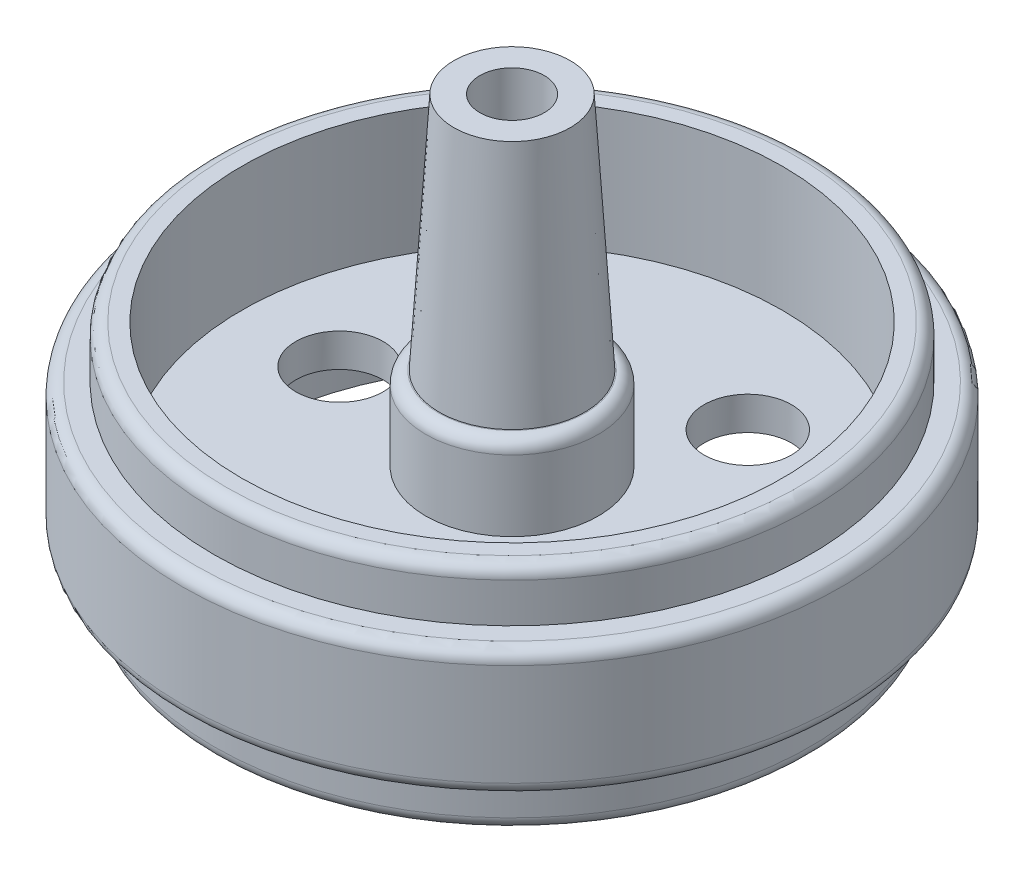
SolidWorks part; units mm, degrees
ref_plane "Front Plane" through (0, 0, 0) normal (0, 0, 1) x (1, 0, 0)
ref_plane "Top Plane" through (0, 0, 0) normal (0, 1, 0) x (1, 0, 0)
ref_plane "Right Plane" through (0, 0, 0) normal (1, 0, 0) x (0, 0, -1)
sketch "Sketch1" plane through (0, 0, 0) normal (0, 1, 0) x (1, 0, 0)
  circle A0 centre (0, 0) radius 14.35
  dimension "D1" = 28.7
extrude "Boss-Extrude1" add sketch "Sketch1" along normal blind 2.5
sketch "Sketch2" plane through (0, 2.5, 0) normal (0, 1, 0) x (1, 0, 0)
  circle A0 centre (0, 0) radius 15.85
  dimension "D1" = 31.7
extrude "Boss-Extrude2" add sketch "Sketch2" along normal blind 6.1
sketch "Sketch4" plane through (0, 8.6, 0) normal (0, 1, 0) x (1, 0, 0)
  circle A0 centre (0, 0) radius 14.35
  dimension "D1" = 28.7
extrude "Boss-Extrude4" add sketch "Sketch4" along normal blind 2.5
sketch "Sketch5" plane through (0, 0, 0) normal (0, -1, 0) x (1, 0, 0)
  circle A0 centre (0, 0) radius 13.05
  circle A1 centre (0, 0) radius 4.3
  dimension "D1" = 26.1
  dimension "D2" = 8.6
sketch "Sketch6" plane through (0, 11.1, 0) normal (0, 1, 0) x (1, 0, 0)
  circle A0 centre (0, 0) radius 13
  dimension "D1" = 26
extrude "Cut-Extrude1" cut sketch "Sketch6" against normal blind 6
extrude "Cut-Extrude2" cut sketch "Sketch5" against normal blind 3.5
sketch "Sketch7" plane through (0, 5.1, 0) normal (0, 1, 0) x (1, 0, 0)
  circle A0 centre (0, 0) radius 4.15
  dimension "D1" = 8.3
extrude "Boss-Extrude5" add sketch "Sketch7" along normal blind 4
sketch "Sketch8" plane through (0, 9.1, 0) normal (0, 1, 0) x (1, 0, 0)
  circle A0 centre (0, 0) radius 3.5
  dimension "D1" = 7
extrude "Boss-Extrude6" add sketch "Sketch8" along normal blind 11.5 draft 3.5
sketch "Sketch9" plane through (0, 0, 0) normal (0, -1, 0) x (1, 0, 0)
  circle A0 centre (0, 0) radius 3.25
  dimension "D1" = 6.5
extrude "Cut-Extrude3" cut sketch "Sketch9" against normal blind 6.65
sketch "Sketch10" plane through (0, 20.6, 0) normal (0, 1, 0) x (1, 0, 0)
  circle A0 centre (0, 0) radius 1.55
  dimension "D1" = 3.1
extrude "Cut-Extrude4" cut sketch "Sketch10" against normal up to next
fillet "Fillet1" radius 0.6 5 edges at (0, 9.1, 4.15) (0, 0, 14.35) (0, 2.5, 15.85) (0, 8.6, 15.85) (0, 11.1, 14.35)
sketch "Sketch11" plane through (0, 5.1, 0) normal (0, 1, 0) x (1, 0, 0)
  circle A0 centre (-8.3, 0) radius 2.1
  circle A1 centre (4.15, 7.188) radius 2.1
  circle A2 centre (0, 0) radius 13 construction
  circle A3 centre (4.15, -7.188) radius 2.1
  point P12 (0, 0)
  dimension "D1" = 4.2
  dimension "D2" = 8.3
  dimension "D5" = 14.376
  dimension "D3" = 0
  dimension "D4" = 3
extrude "Cut-Extrude5" cut sketch "Sketch11" against normal through all
